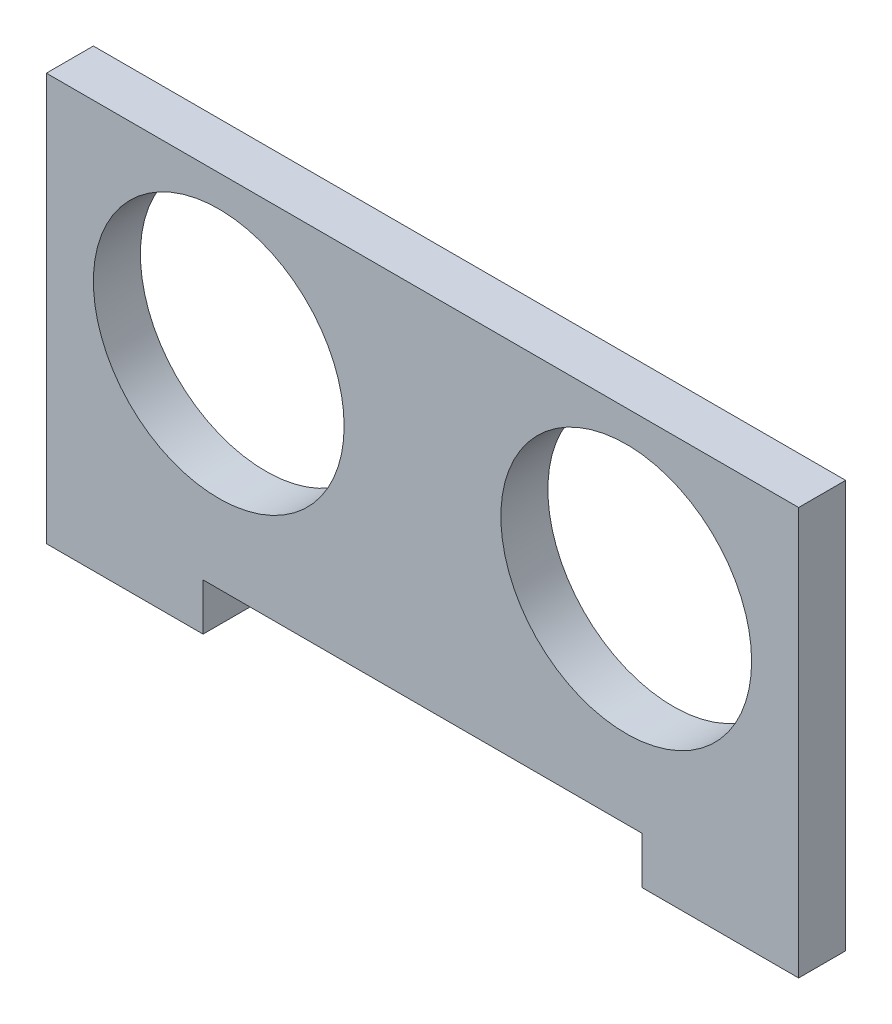
SolidWorks part; units mm, degrees
ref_plane "Alzado" through (0, 0, 0) normal (0, 0, 1) x (1, 0, 0)
ref_plane "Planta" through (0, 0, 0) normal (0, 1, 0) x (1, 0, 0)
ref_plane "Vista lateral" through (0, 0, 0) normal (1, 0, 0) x (0, 0, -1)
sketch "Model" plane through (0, 0, 0) normal (0, 0, 1) x (1, 0, 0)
  line L0 (42.2, 7.5) -> (14.2, 7.5)
  line L1 (4.2, 30.5) -> (52.2, 30.5)
  line L2 (42.2, 4.5) -> (42.2, 7.5)
  line L3 (14.2, 4.5) -> (14.2, 7.5)
  line L4 (52.2, 30.5) -> (52.2, 4.5)
  line L5 (4.2, 30.5) -> (4.2, 4.5)
  line L6 (42.2, 4.5) -> (52.2, 4.5)
  line L7 (4.2, 4.5) -> (14.2, 4.5)
  circle A0 centre (41.2, 20.5) radius 8
  circle A1 centre (15.2, 20.5) radius 8
extrude "Saliente-Extruir1" add sketch "Model" along normal blind 3
